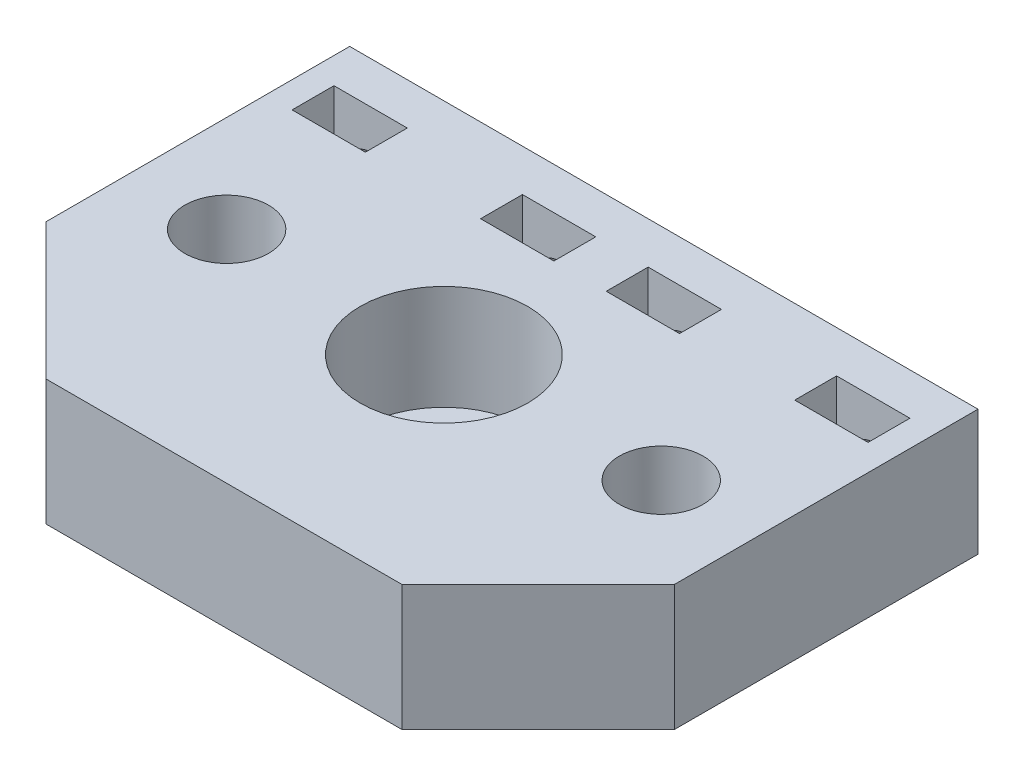
SolidWorks part; units mm, degrees
ref_plane "Front Plane" through (0, 0, 0) normal (0, 0, 1) x (1, 0, 0)
ref_plane "Top Plane" through (0, 0, 0) normal (0, 1, 0) x (1, 0, 0)
ref_plane "Right Plane" through (0, 0, 0) normal (1, 0, 0) x (0, 0, -1)
sketch "Sketch1" plane through (0, 0, 0) normal (0, 1, 0) x (1, 0, 0)
  line L1 (-30, -21) -> (30, -21)
  line L2 (-30, -21) -> (-30, 21)
  line L3 (-30, 21) -> (30, 21)
  line L4 (30, -21) -> (30, 21)
  line L5 (-30, -21) -> (30, 21) construction
  line L6 (-30, 21) -> (30, -21) construction
  point P0 (0, 0)
  dimension "D1" = 60
  dimension "D2" = 42
extrude "Boss-Extrude1" add sketch "Sketch1" along normal blind 12
sketch "Sketch2" plane through (0, 12, 0) normal (0, 1, 0) x (1, 0, 0)
  circle A0 centre (0, 0) radius 4
  dimension "D1" = 8
extrude "Cut-Extrude1" cut sketch "Sketch2" against normal up to next and the other way through all
sketch "Sketch3" plane through (0, 12, 0) normal (0, 1, 0) x (1, 0, 0)
  line L0 (0, 21) -> (0, -21) construction
  line L1 (30, 21) -> (-30, 21) construction
  line L2 (-30, -21) -> (30, -21) construction
  line L3 (0, 0) -> (30, 0) construction
  line L4 (30, -21) -> (30, 21) construction
  circle A0 centre (0, 0) radius 8
  circle A1 centre (20.75, 0) radius 4
  circle A2 centre (-20.75, 0) radius 4
  dimension "D1" = 16
  dimension "D2" = 20.75
  dimension "D3" = 8
extrude "Cut-Extrude2" cut sketch "Sketch3" against normal blind 10 and the other way through all
chamfer "Chamfer1" distance 13 angle 45 2 edges at (30, 6, 21) (-30, 6, 21)
sketch "Sketch5" plane through (0, 12, 0) normal (0, 1, 0) x (1, 0, 0)
  line L0 (30, 15) -> (-30, 15) construction
  line L1 (30, -8) -> (30, 21) construction
  line L2 (-30, 21) -> (-30, -8) construction
  line L3 (30, 21) -> (-30, 21) construction
  line L4 (27.5, 17) -> (20.5, 17)
  line L5 (27.5, 17) -> (27.5, 13)
  line L6 (27.5, 13) -> (20.5, 13)
  line L7 (20.5, 17) -> (20.5, 13)
  line L8 (27.5, 17) -> (20.5, 13) construction
  line L9 (27.5, 13) -> (20.5, 17) construction
  line L10 (9.5, 17) -> (9.5, 13)
  line L11 (9.5, 17) -> (2.5, 17)
  line L12 (2.5, 17) -> (2.5, 13)
  line L13 (9.5, 13) -> (2.5, 13)
  line L14 (0, 21) -> (0, 0) construction
  line L15 (-9.5, 17) -> (-2.5, 17)
  line L16 (-2.5, 17) -> (-2.5, 13)
  line L17 (-9.5, 13) -> (-2.5, 13)
  line L18 (-9.5, 17) -> (-9.5, 13)
  line L19 (-27.5, 13) -> (-20.5, 13)
  line L20 (-20.5, 17) -> (-20.5, 13)
  line L21 (-27.5, 17) -> (-20.5, 17)
  line L22 (-27.5, 17) -> (-27.5, 13)
  point P6 (24, 15)
  dimension "D1" = 7
  dimension "D2" = 4
  dimension "D3" = 6
  dimension "D4" = 6
  dimension "D6" = 18
  dimension "D5" = 2
extrude "Cut-Extrude4" cut sketch "Sketch5" against normal up to next and the other way through all
sketch "Sketch4" plane through (0, 0, -21) normal (0, 0, -1) x (-1, 0, 0)
  line L0 (-30, 6) -> (30, 6) construction
  line L1 (-30, 12) -> (-30, 0) construction
  line L2 (30, 12) -> (30, 0) construction
  line L4 (0, 0) -> (0, 12) construction
  line L5 (-30, 12) -> (30, 12) construction
  circle A0 centre (-24, 6) radius 2.25
  circle A1 centre (-6, 6) radius 2.25
  circle A2 centre (6, 6) radius 2.25
  circle A3 centre (24, 6) radius 2.25
  dimension "D1" = 4.5
  dimension "D2" = 6
  dimension "D4" = 18
  dimension "D3" = 2
extrude "Cut-Extrude3" cut sketch "Sketch4" against normal blind 7.5
